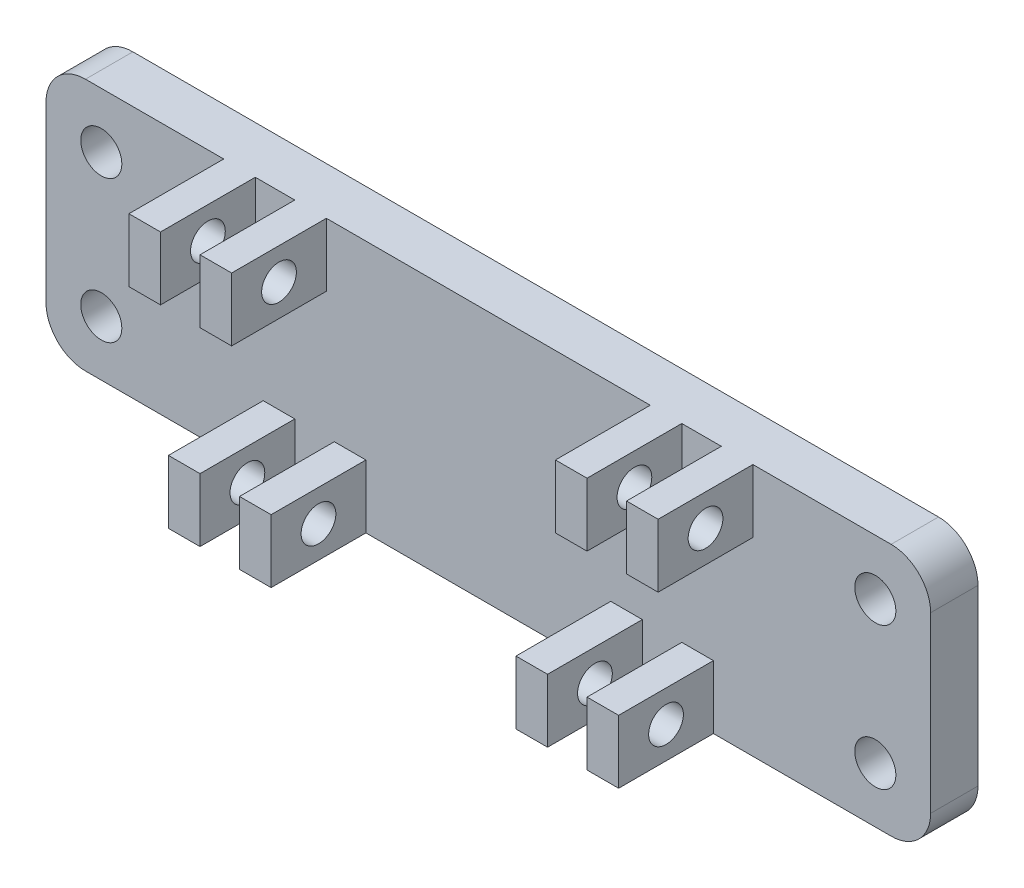
SolidWorks part; units mm, degrees
ref_plane "前视基准面" through (0, 0, 0) normal (0, 0, 1) x (1, 0, 0)
ref_plane "上视基准面" through (0, 0, 0) normal (0, 1, 0) x (1, 0, 0)
ref_plane "右视基准面" through (0, 0, 0) normal (1, 0, 0) x (0, 0, -1)
sketch "草图2" plane through (0, 0, 0) normal (0, 0, 1) x (1, 0, 0)
  line L0 (52.5, -4.5) -> (-3.5, -4.5) construction
  line L1 (-1, -12.5) -> (50, -12.5)
  line L2 (-3.5, -10) -> (-3.5, 1)
  line L3 (-1, 3.5) -> (50, 3.5)
  line L4 (-1, -81.5) -> (50, -81.5)
  line L5 (52.5, -79) -> (52.5, 1)
  line L6 (50, 3.5) -> (-1, 3.5)
  line L7 (-3.5, 1) -> (-3.5, -79)
  line L8 (-1, -81.5) -> (50, -81.5)
  line L9 (52.5, -10) -> (52.5, 1)
  line L10 (50, 3.5) -> (-1, 3.5)
  line L11 (-3.5, 1) -> (-3.5, -79)
  line L12 (52.5, -12.5) -> (52.5, 1)
  circle A0 centre (49, 0) radius 1.3
  circle A1 centre (0, 0) radius 1.3
  arc A2 (-1, 3.5) -> (-3.5, 1) centre (-1, 1) ccw
  arc A3 (52.5, 1) -> (50, 3.5) centre (50, 1) ccw
  arc A4 (-3.5, -79) -> (-1, -81.5) centre (-1, -79) ccw
  arc A5 (50, -81.5) -> (52.5, -79) centre (50, -79) ccw
  arc A6 (52.5, 1) -> (50, 3.5) centre (50, 1) ccw
  arc A7 (-1, 3.5) -> (-3.5, 1) centre (-1, 1) ccw
  arc A8 (-3.5, -79) -> (-1, -81.5) centre (-1, -79) ccw
  arc A9 (50, -81.5) -> (52.5, -79) centre (50, -79) ccw
  arc A10 (52.5, 1) -> (50, 3.5) centre (50, 1) ccw
  arc A11 (-1, 3.5) -> (-3.5, 1) centre (-1, 1) ccw
  arc A12 (50, -12.5) -> (52.5, -10) centre (50, -10) ccw
  arc A13 (-3.5, -10) -> (-1, -12.5) centre (-1, -10) ccw
  circle A14 centre (0, -9) radius 1.3
  circle A15 centre (49, -9) radius 1.3
  point P31 (-3.5, -12.5)
  line M16 (52.5, -79) -> (52.5, 1)
  arc M17 (52.5, 1) -> (50, 3.5) centre (50, 1) ccw
  line M18 (50, 3.5) -> (-1, 3.5)
  arc M19 (-1, 3.5) -> (-3.5, 1) centre (-1, 1) ccw
  line M20 (-3.5, 1) -> (-3.5, -79)
  circle M21 centre (49, 0) radius 1.3
  circle M22 centre (0, 0) radius 1.3
  dimension "D4" = 2.6
  dimension "D5" = 2.6
  dimension "D6" = 2.5
  dimension "D7" = 2.5
  dimension "D8" = 2.5
  dimension "D9" = 2.5
  dimension "D2" = 16
  dimension "D3" = 0
  dimension "D1" = 0
extrude "凸台-拉伸2" add sketch "草图2" along normal blind 3 contours L1 M20 M16 M17 M18 M19 M22 M21 | L0 L11 A13 L1 A12 A15 A14 M16
sketch "草图4" plane through (0, 0, 3) normal (0, 0, 1) x (1, 0, 0)
  line L0 (24.5, 3.5) -> (24.5, -12.5) construction
  line L1 (7.75, 1.5) -> (14.25, 1.5) construction
  line L4 (-3.5, 1) -> (-3.5, -10)
  line L5 (-1, -12.5) -> (50, -12.5)
  line L6 (52.5, -10) -> (52.5, 1)
  line L7 (50, 3.5) -> (-1, 3.5)
  line L8 (-3.5, 1) -> (-3.5, -10)
  line L10 (52.5, -10) -> (52.5, 1)
  line L11 (50, 3.5) -> (-1, 3.5)
  line L14 (7.75, 3.5) -> (14.25, 3.5)
  line L15 (7.75, 3.5) -> (7.75, -0.5)
  line L16 (7.75, -0.5) -> (14.25, -0.5)
  line L17 (14.25, 3.5) -> (14.25, -0.5)
  line L18 (39.25, -0.5) -> (36.75, 3.5) construction
  line L19 (9.75, 3.5) -> (12.25, 3.5)
  line L20 (9.75, 3.5) -> (9.75, -0.5)
  line L21 (9.75, -0.5) -> (12.25, -0.5)
  line L22 (12.25, 3.5) -> (12.25, -0.5)
  line L23 (9.75, 3.5) -> (12.25, -0.5) construction
  line L24 (9.75, -0.5) -> (12.25, 3.5) construction
  line L25 (39.25, 3.5) -> (36.75, -0.5) construction
  line L26 (41.25, 1.5) -> (34.75, 1.5) construction
  line L27 (36.75, 3.5) -> (36.75, -0.5)
  line L28 (39.25, -0.5) -> (36.75, -0.5)
  line L29 (39.25, 3.5) -> (39.25, -0.5)
  line L30 (39.25, 3.5) -> (36.75, 3.5)
  line L31 (34.75, 3.5) -> (34.75, -0.5)
  line L32 (41.25, -0.5) -> (34.75, -0.5)
  line L33 (41.25, 3.5) -> (41.25, -0.5)
  line L34 (41.25, 3.5) -> (34.75, 3.5)
  line L35 (10.25, -10.5) -> (16.75, -10.5) construction
  line L36 (10.25, -12.5) -> (16.75, -12.5)
  line L37 (10.25, -12.5) -> (10.25, -8.5)
  line L38 (10.25, -8.5) -> (16.75, -8.5)
  line L39 (16.75, -12.5) -> (16.75, -8.5)
  line L40 (36.75, -8.5) -> (34.25, -12.5) construction
  line L41 (12.25, -12.5) -> (14.75, -12.5)
  line L42 (12.25, -12.5) -> (12.25, -8.5)
  line L43 (12.25, -8.5) -> (14.75, -8.5)
  line L44 (14.75, -12.5) -> (14.75, -8.5)
  line L45 (12.25, -12.5) -> (14.75, -8.5) construction
  line L46 (12.25, -8.5) -> (14.75, -12.5) construction
  line L47 (36.75, -12.5) -> (34.25, -8.5) construction
  line L48 (38.75, -10.5) -> (32.25, -10.5) construction
  line L49 (34.25, -12.5) -> (34.25, -8.5)
  line L50 (36.75, -8.5) -> (34.25, -8.5)
  line L51 (36.75, -12.5) -> (36.75, -8.5)
  line L52 (36.75, -12.5) -> (34.25, -12.5)
  line L53 (32.25, -12.5) -> (32.25, -8.5)
  line L54 (38.75, -8.5) -> (32.25, -8.5)
  line L55 (38.75, -12.5) -> (38.75, -8.5)
  line L56 (38.75, -12.5) -> (32.25, -12.5)
  line L62 (-1, -12.5) -> (50, -12.5)
  arc A2 (52.5, 1) -> (50, 3.5) centre (50, 1) ccw
  arc A3 (-1, 3.5) -> (-3.5, 1) centre (-1, 1) ccw
  arc A4 (52.5, 1) -> (50, 3.5) centre (50, 1) ccw
  arc A5 (-1, 3.5) -> (-3.5, 1) centre (-1, 1) ccw
  arc A8 (-3.5, -10) -> (-1, -12.5) centre (-1, -10) ccw
  arc A10 (-3.5, -10) -> (-1, -12.5) centre (-1, -10) ccw
  arc A12 (50, -12.5) -> (52.5, -10) centre (50, -10) ccw
  arc A13 (50, -12.5) -> (52.5, -10) centre (50, -10) ccw
  point P16 (11, 1.5)
  point P31 (38, 1.5)
  point P38 (13.5, -10.5)
  point P53 (35.5, -10.5)
  line M10 (-1, -12.5) -> (50, -12.5)
  dimension "D2" = 4
  dimension "D3" = 6.5
  dimension "D4" = 2.5
  dimension "D5" = 27
  dimension "D6" = 2.5
  dimension "D7" = 6.5
  dimension "D8" = 0
  dimension "D1" = 0
extrude "凸台-拉伸3" add sketch "草图4" along normal blind 6 contours L20 L11 L15 L16 | L11 L22 L16 L17 | L32 L27 L11 L31 | L33 L11 L29 L32 | L62 L42 L38 L37 | L44 L62 L39 L38 | L49 L54 L53 L62 | L55 L54 L51 M10
sketch "草图6" plane through (7.75, 0, 0) normal (-1, 0, 0) x (0, 0, 1)
  line L0 (9, 3.5) -> (3, -0.5) construction
  line L1 (9, -8.5) -> (3, -12.5) construction
  line L4 (3, 3.5) -> (3, -0.5)
  line L5 (3, -0.5) -> (9, -0.5)
  line L6 (9, -0.5) -> (9, 3.5)
  line L7 (9, 3.5) -> (3, 3.5)
  line L8 (3, 3.5) -> (3, -0.5)
  line L9 (3, -0.5) -> (9, -0.5)
  line L10 (9, -0.5) -> (9, 3.5)
  line L11 (9, 3.5) -> (3, 3.5)
  line L12 (3, -8.5) -> (3, -12.5)
  line L13 (3, -12.5) -> (9, -12.5)
  line L14 (9, -12.5) -> (9, -8.5)
  line L15 (9, -8.5) -> (3, -8.5)
  line L16 (3, -8.5) -> (3, -12.5)
  line L17 (3, -12.5) -> (9, -12.5)
  line L18 (9, -12.5) -> (9, -8.5)
  line L19 (9, -8.5) -> (3, -8.5)
  circle A0 centre (6, 1.5) radius 1.1
  circle A1 centre (6, -10.5) radius 1.1
  dimension "D3" = 2.2
  dimension "D4" = 2.2
  dimension "D1" = 0
  dimension "D2" = 0
extrude "切除-拉伸2" cut sketch "草图6" against normal through all contours A0 | A1
